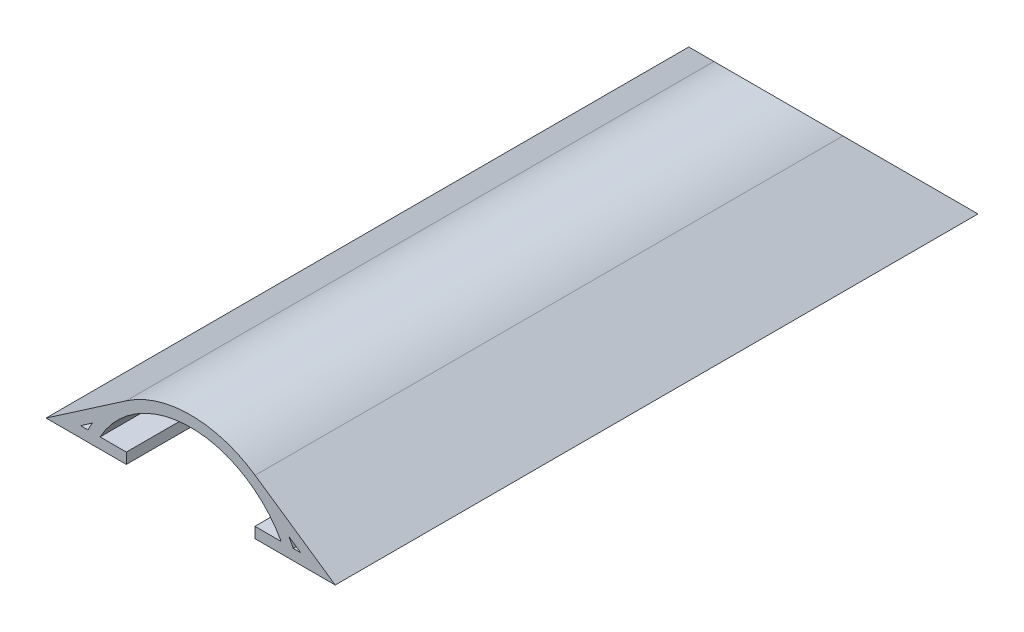
SolidWorks part; units mm, degrees
material "PUR"
ref_plane "Front Plane" through (0, 0, 0) normal (0, 0, 1) x (1, 0, 0)
ref_plane "Top Plane" through (0, 0, 0) normal (0, 1, 0) x (1, 0, 0)
ref_plane "Right Plane" through (0, 0, 0) normal (1, 0, 0) x (0, 0, -1)
sketch "Sketch2" plane through (0, 0, 0) normal (0, 0, 1) x (1, 0, 0)
  line L0 (0, 0) -> (68.58, 0)
  line L1 (34.29, 0) -> (34.29, 17.78) construction
  line L2 (18.9927, 13.0354) -> (0, 0)
  line L3 (49.5873, 13.0354) -> (68.58, 0)
  line L4 (10.9978, 4.4675) -> (8.1894, 2.54)
  line L5 (8.1894, 2.54) -> (9.965, 2.54)
  line L6 (57.5822, 4.4675) -> (60.3906, 2.54)
  line L7 (20.43, 10.9412) -> (8.1894, 2.54) construction
  line L8 (48.15, 10.9412) -> (60.3906, 2.54) construction
  line L9 (12.8231, 2.54) -> (55.7569, 2.54)
  line L10 (8.1894, 2.54) -> (60.3906, 2.54) construction
  line L11 (58.615, 2.54) -> (60.3906, 2.54)
  arc A0 (58.615, 2.54) -> (57.5822, 4.4675) centre (34.29, -9.2529) ccw
  arc A1 (55.7569, 2.54) -> (12.8231, 2.54) centre (34.29, -9.2529) ccw
  circle A2 centre (34.29, -9.2529) radius 27.0329 construction
  circle A3 centre (34.29, -9.2529) radius 24.4929 construction
  arc A4 (10.9978, 4.4675) -> (9.965, 2.54) centre (34.29, -9.2529) ccw
  arc A5 (49.5873, 13.0354) -> (18.9927, 13.0354) centre (34.29, -9.2529) ccw
  point P7 (59.69, 0)
  dimension "D1" = 68.58
  dimension "D2" = 17.78
  dimension "D3" = 8.89
  dimension "D4" = 2.54
  dimension "D5" = 2.54
extrude "Boss-Extrude1" add sketch "Sketch2" along normal blind 152.4
sketch "Sketch3" plane through (0, 0, 0) normal (1, 0, 0) x (0, 0, -1)
  line L0 (-17.78, 17.78) -> (0, 0)
  line L1 (0, 0) -> (0, 17.78)
  line L2 (0, 17.78) -> (-17.78, 17.78)
  line L3 (0, 13.0354) -> (0, 0) construction
  line L4 (0, 13.0354) -> (0, 17.78) construction
  line L5 (0, 13.0354) -> (0, 0) construction
  line L6 (0, 13.0354) -> (0, 17.78) construction
  dimension "D1" = 45
extrude "Cut-Extrude1" cut sketch "Sketch3" along normal through all
sketch "Sketch4" plane through (0, 0, 0) normal (0, -1, 0) x (1, 0, 0)
  line L6 (0, 152.4) -> (0, 0) construction
  line L7 (19.05, 152.4) -> (49.53, 152.4)
  line L8 (19.05, 152.4) -> (19.05, 114.3)
  line L9 (19.05, 114.3) -> (49.53, 114.3)
  line L10 (49.53, 152.4) -> (49.53, 114.3)
  line L11 (68.58, 152.4) -> (68.58, 0) construction
  line L12 (0, 152.4) -> (68.58, 152.4) construction
  dimension "D1" = 19.05
  dimension "D2" = 19.05
  dimension "D3" = 0
  dimension "D4" = 38.1
extrude "Cut-Extrude2" cut sketch "Sketch4" against normal up to next
